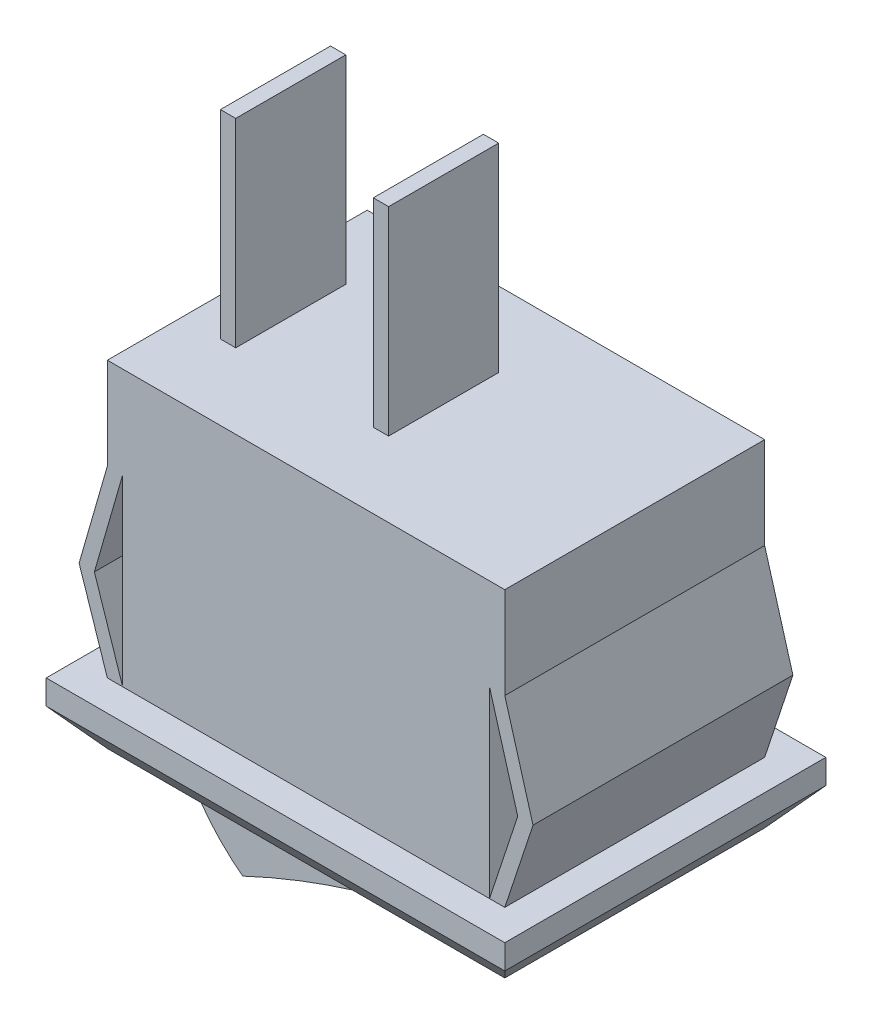
SolidWorks part; units mm, degrees
ref_plane "前视基准面" through (0, 0, 0) normal (0, 0, 1) x (1, 0, 0)
ref_plane "上视基准面" through (0, 0, 0) normal (0, 1, 0) x (1, 0, 0)
ref_plane "右视基准面" through (0, 0, 0) normal (1, 0, 0) x (0, 0, -1)
sketch "草图1" plane through (0, 0, 0) normal (0, 1, 0) x (1, 0, 0)
  line L1 (-7.5, 5.25) -> (7.5, 5.25)
  line L2 (-7.5, 5.25) -> (-7.5, -5.25)
  line L3 (-7.5, -5.25) -> (7.5, -5.25)
  line L4 (7.5, 5.25) -> (7.5, -5.25)
  line L5 (-7.5, 5.25) -> (7.5, -5.25) construction
  line L6 (-7.5, -5.25) -> (7.5, 5.25) construction
  point P0 (0, 0)
  dimension "D1" = 15
  dimension "D2" = 10.5
extrude "凸台-拉伸1" add sketch "草图1" along normal blind 0.8
ref_plane "基准面1" through (0, -1.2, 0) normal (0, -1, 0) x (-1, 0, 0)
sketch "草图2" plane through (0, -1.2, 0) normal (0, -1, 0) x (-1, 0, 0)
  line L1 (6.5, -4.25) -> (-6.5, -4.25)
  line L2 (6.5, -4.25) -> (6.5, 4.25)
  line L3 (6.5, 4.25) -> (-6.5, 4.25)
  line L4 (-6.5, -4.25) -> (-6.5, 4.25)
  line L5 (6.5, -4.25) -> (-6.5, 4.25) construction
  line L6 (6.5, 4.25) -> (-6.5, -4.25) construction
  point P0 (0, 0)
  dimension "D1" = 13
  dimension "D2" = 8.5
loft "放样1" add profiles "草图2" section "草图2" section face at (0, 0, 0)
sketch "草图3" plane through (0, 0, 0) normal (0, 0, 1) x (1, 0, 0)
  line L0 (7.5, 0.8) -> (-7.5, 0.8) construction
  line L1 (7.5, 0.8) -> (-7.5, 0.8) construction
  line L2 (0, -2.4046) -> (0, 3.2696) construction
  line L3 (0, 0.8) -> (0, 9.8) construction
  line L4 (6.5, 9.8) -> (-6.5, 9.8)
  line L5 (-6.5, 9.8) -> (-6.5, 6.8)
  line L6 (-6.5, 6.8) -> (-6, 6.8)
  line L7 (-6, 6.8) -> (-6, 0.8)
  line L8 (-6, 0.8) -> (6, 0.8)
  line L9 (6, 6.8) -> (6, 0.8)
  line L10 (6.5, 6.8) -> (6, 6.8)
  line L11 (6.5, 9.8) -> (6.5, 6.8)
  dimension "D1" = 9
  dimension "D2" = 6
  dimension "D3" = 6.5
  dimension "D4" = 3
extrude "凸台-拉伸2" add sketch "草图3" along normal mid plane 8.5 contours L8 L9 L10 L11 L4 L5 L6 L7
sketch "草图4" plane through (0, 0, -4.25) normal (0, 0, -1) x (-1, 0, 0)
  line L0 (6.5, 6.8) -> (7.4237, 3.5911)
  line L1 (7.4237, 3.5911) -> (6.5, 0.8)
  line L2 (-7.5, 0.8) -> (7.5, 0.8) construction
  line L3 (6.5, 0.8) -> (6, 0.8)
  line L4 (6, 0.8) -> (6.9237, 3.5911)
  line L5 (6.9237, 3.5911) -> (6, 6.8)
  line L6 (6, 6.8) -> (6.5, 6.8)
  line L8 (0, -3.0899) -> (0, 9.0599) construction
  line L9 (-6, 6.8) -> (-6.5, 6.8)
  line L10 (-6.9237, 3.5911) -> (-6, 6.8)
  line L11 (-6, 0.8) -> (-6.9237, 3.5911)
  line L12 (-6.5, 0.8) -> (-6, 0.8)
  line L13 (-7.4237, 3.5911) -> (-6.5, 0.8)
  line L14 (-6.5, 6.8) -> (-7.4237, 3.5911)
extrude "凸台-拉伸4" add sketch "草图4" against normal blind 8.5 contours L6 L0 L1 L3 L4 L5 | L9 L14 L13 L12 L11 L10
sketch "草图5" plane through (0, 9.8, 0) normal (0, 1, 0) x (1, 0, 0)
  line L1 (-0.25, 1.8) -> (0.25, 1.8)
  line L2 (-0.25, 1.8) -> (-0.25, -1.8)
  line L3 (-0.25, -1.8) -> (0.25, -1.8)
  line L4 (0.25, 1.8) -> (0.25, -1.8)
  line L5 (-0.25, 1.8) -> (0.25, -1.8) construction
  line L6 (-0.25, -1.8) -> (0.25, 1.8) construction
  line L7 (-5.25, 1.8) -> (-4.75, 1.8)
  line L8 (-5.25, 1.8) -> (-5.25, -1.8)
  line L9 (-5.25, -1.8) -> (-4.75, -1.8)
  line L10 (-4.75, 1.8) -> (-4.75, -1.8)
  line L11 (-5.25, 1.8) -> (-4.75, -1.8) construction
  line L12 (-5.25, -1.8) -> (-4.75, 1.8) construction
  point P0 (0, 0)
  point P6 (-5, 0)
  dimension "D1" = 3.6
  dimension "D2" = 0.5
  dimension "D3" = 5
  dimension "D4" = 0.5
  dimension "D5" = 3.6
extrude "凸台-拉伸5" add sketch "草图5" along normal blind 6.5 contours L4 L1 L2 L3 | L8 L7 L10 L9
sketch "草图6" plane through (0, -1.2, 0) normal (0, -1, 0) x (-1, 0, 0)
  line L0 (-6.5, -4.25) -> (6.5, -4.25) construction
  line L1 (5.5, -3.25) -> (-5.5, -3.25)
  line L2 (5.5, -3.25) -> (5.5, 3.25)
  line L3 (5.5, 3.25) -> (-5.5, 3.25)
  line L4 (-5.5, -3.25) -> (-5.5, 3.25)
  line L5 (5.5, -3.25) -> (-5.5, 3.25) construction
  line L6 (5.5, 3.25) -> (-5.5, -3.25) construction
  line L7 (-6.5, 4.25) -> (-6.5, -4.25) construction
  point P0 (0, 0)
  dimension "D1" = 1
  dimension "D2" = 1
extrude "切除-拉伸1" cut sketch "草图6" against normal blind 1 contours L2 L1 L4 L3
sketch "草图7" plane through (0, 0, 0) normal (0, 0, 1) x (1, 0, 0)
  line L0 (-5.5, -0.2) -> (5.5, -0.2)
  line L1 (-55, -1.2) -> (55, -1.2) construction
  line L2 (0, -2.2142) -> (0, 2.9231) construction
  line L3 (5.5, -1.2) -> (5.5, -0.2)
  arc A0 (-5.5, -0.2) -> (-3.174, -3.7) centre (0.6442, 1.3604) ccw
  arc A1 (-3.174, -3.7) -> (5.5, -1.2) centre (8.8876, -29.2514) cw
  dimension "D1" = 1
  dimension "D2" = 2.5
extrude "凸台-拉伸6" add sketch "草图7" along normal mid plane 6.3 contours L3 L0 A0 A1
